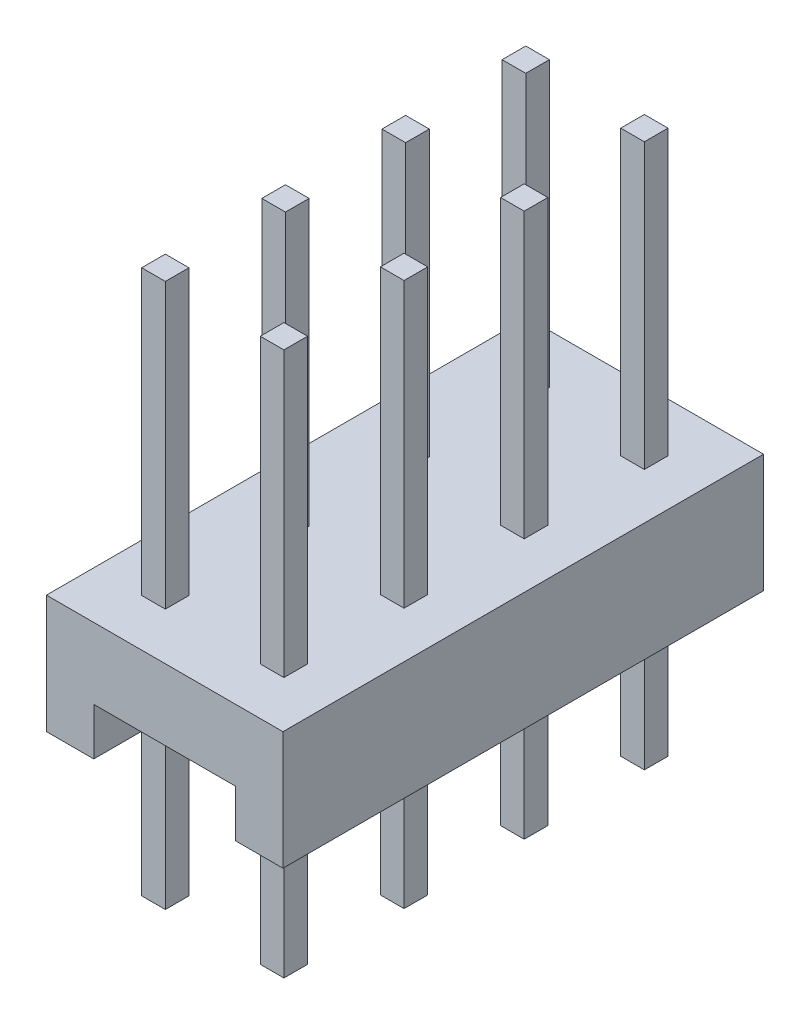
SolidWorks part; units mm, degrees
ref_plane "Спереди" through (0, 0, 0) normal (0, 0, 1) x (1, 0, 0)
ref_plane "Сверху" through (0, 0, 0) normal (0, 1, 0) x (1, 0, 0)
ref_plane "Справа" through (0, 0, 0) normal (1, 0, 0) x (0, 0, -1)
sketch "Эскиз1" plane through (0, 0, 0) normal (0, 0, 1) x (1, 0, 0)
  line L0 (-2.5, 0) -> (-2.5, 2.5)
  line L1 (-2.5, 2.5) -> (2.5, 2.5)
  line L2 (2.5, 2.5) -> (2.5, 0)
  line L3 (-2.5, 0) -> (-1.5, 0)
  line L4 (-1.5, 0) -> (-1.5, 1)
  line L5 (-1.5, 1) -> (1.5, 1)
  line L6 (1.5, 1) -> (1.5, 0)
  line L7 (1.5, 0) -> (2.5, 0)
  line L8 (-2.5, 0) -> (2.5, 0) construction
  dimension "D1" = 2.5
  dimension "D2" = 5
  dimension "D3" = 1
  dimension "D4" = 1
  dimension "D5" = 1
  dimension "D6" = 2.5
extrude "Бобышка-Вытянуть1" add sketch "Эскиз1" along normal blind 2.54
sketch "Эскиз2" plane through (0, 2.5, 0) normal (0, 1, 0) x (1, 0, 0)
  line L0 (-2.5, -1.27) -> (2.5, -1.27) construction
  line L1 (-1.4869, -1.04) -> (-0.9869, -1.04)
  line L2 (-1.4869, -1.04) -> (-1.4869, -1.54)
  line L3 (-1.4869, -1.54) -> (-0.9869, -1.54)
  line L4 (-0.9869, -1.04) -> (-0.9869, -1.54)
  line L5 (1.02, -1.04) -> (1.52, -1.04)
  line L6 (1.02, -1.04) -> (1.02, -1.54)
  line L7 (1.02, -1.54) -> (1.52, -1.54)
  line L8 (1.52, -1.04) -> (1.52, -1.54)
  line L9 (-2.5, -2.54) -> (-2.5, 0) construction
  line L10 (2.5, -2.54) -> (2.5, 0) construction
  line L11 (2.5, 0) -> (-2.5, 0) construction
  line L12 (-1.27, 0) -> (-1.27, -2.54) construction
  line L13 (2.5, -2.54) -> (-2.5, -2.54) construction
  line L14 (1.27, 0) -> (1.27, -2.54) construction
  dimension "D1" = 0.5
  dimension "D2" = 0.5
  dimension "D3" = 0.5
  dimension "D4" = 0.5
  dimension "D5" = 2.54
  dimension "D6" = 1.0131
  dimension "D7" = 1.23
  dimension "D8" = 1.27
  dimension "D9" = 1
  dimension "D10" = 1
  dimension "D11" = 0.25
extrude "Бобышка-Вытянуть2" add sketch "Эскиз2" along normal blind 6 and the other way blind 5.5
pattern_linear "Линейный массив1" count 4 spacing 2.54 along (0, 0, -1) of "Бобышка-Вытянуть1", "Бобышка-Вытянуть2"
